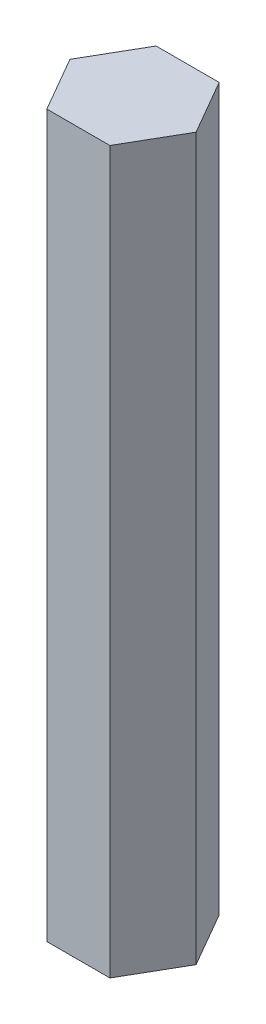
SolidWorks part; units mm, degrees
ref_plane "Front Plane" through (0, 0, 0) normal (0, 0, 1) x (1, 0, 0)
ref_plane "Top Plane" through (0, 0, 0) normal (0, 1, 0) x (1, 0, 0)
ref_plane "Right Plane" through (0, 0, 0) normal (1, 0, 0) x (0, 0, -1)
sketch "Sketch1" plane through (0, 0, 0) normal (0, 1, 0) x (1, 0, 0)
  line L1 (3.6662, 6.35) -> (-3.6662, 6.35)
  line L2 (-3.6662, 6.35) -> (-7.3323, 0)
  line L3 (-7.3323, 0) -> (-3.6662, -6.35)
  line L4 (-3.6662, -6.35) -> (3.6662, -6.35)
  line L5 (3.6662, -6.35) -> (7.3323, 0)
  line L6 (7.3323, 0) -> (3.6662, 6.35)
  circle A0 centre (0, 0) radius 6.35 construction
  dimension "D1" = 12.7
extrude "Boss-Extrude1" add sketch "Sketch1" along normal blind 83.82
